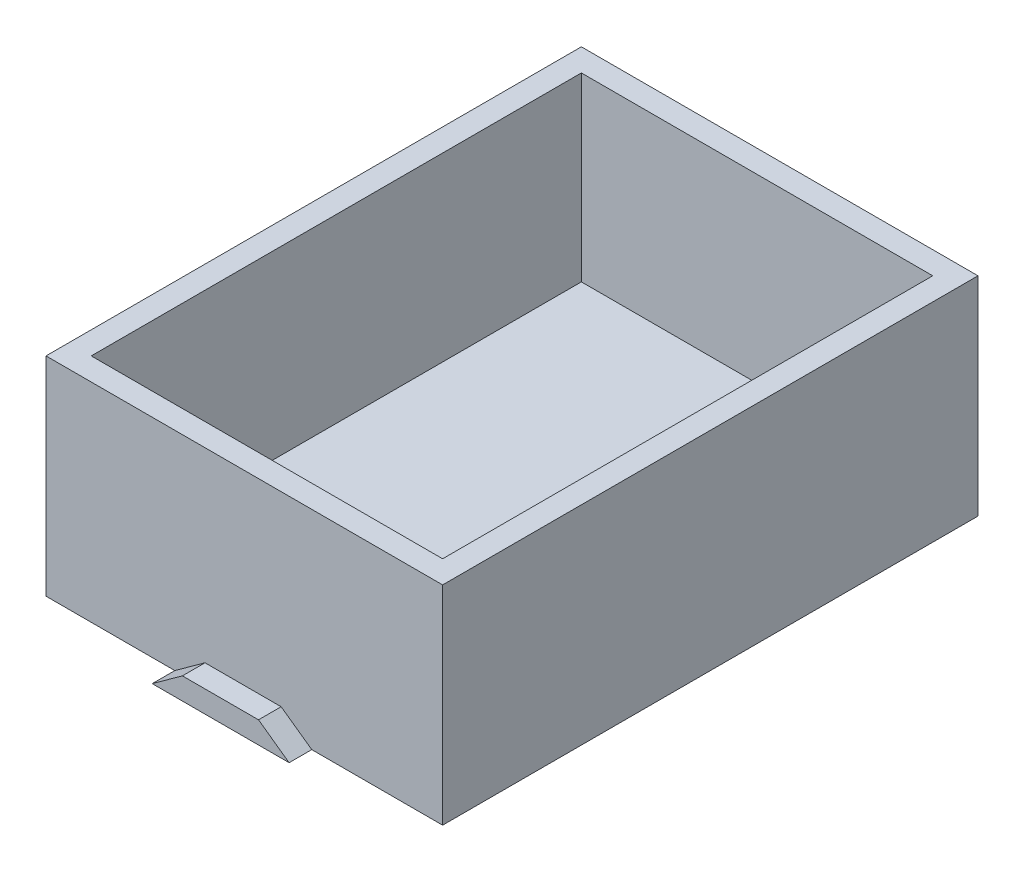
SolidWorks part; units mm, degrees
ref_plane "Front Plane" through (0, 0, 0) normal (0, 0, 1) x (1, 0, 0)
ref_plane "Top Plane" through (0, 0, 0) normal (0, 1, 0) x (1, 0, 0)
ref_plane "Right Plane" through (0, 0, 0) normal (1, 0, 0) x (0, 0, -1)
sketch "Sketch1" plane through (0, 0, 0) normal (0, 0, 1) x (1, 0, 0)
  line L0 (0, 0) -> (66.802, 0)
  line L1 (0, 0) -> (0, 35.052)
  line L2 (0, 35.052) -> (66.802, 35.052)
  line L3 (66.802, 35.052) -> (66.802, 0)
extrude "Boss-Extrude1" add sketch "Sketch1" against normal blind 90.17
sketch "Sketch2" plane through (0, 35.052, 0) normal (0, 1, 0) x (1, 0, 0)
  line L0 (3.81, 3.81) -> (3.81, 86.36)
  line L1 (0, 0) -> (66.802, 0)
  line L2 (0, 0) -> (0, 90.17)
  line L3 (0, 90.17) -> (66.802, 90.17)
  line L4 (66.802, 0) -> (66.802, 90.17)
  line L5 (3.81, 86.36) -> (62.992, 86.36)
  line L6 (62.992, 3.81) -> (62.992, 86.36)
  line L7 (3.81, 3.81) -> (62.992, 3.81)
  point P10 (0, 0)
  point P11 (0, 0)
  dimension "D1" = 3.81
extrude "Cut-Extrude2" cut sketch "Sketch2" against normal blind 30.48 contours L0 L5 L6 L7
sketch "Sketch3" plane through (0, 0, 0) normal (0, 0, 1) x (1, 0, 0)
  line L0 (21.6955, 0) -> (44.7581, 0)
  line L3 (33.2268, 0) -> (44.7581, 0)
  line L4 (44.7581, 0) -> (39.6021, 3.6794)
  line L5 (39.6021, 3.6794) -> (26.7818, 3.6794)
  line L6 (26.7818, 3.6794) -> (21.6955, 0)
  line M2 (0, 0) -> (66.802, 0)
extrude "Boss-Extrude2" add sketch "Sketch3" along normal blind 3.81 contours L5 L6 L0 L4 M2
